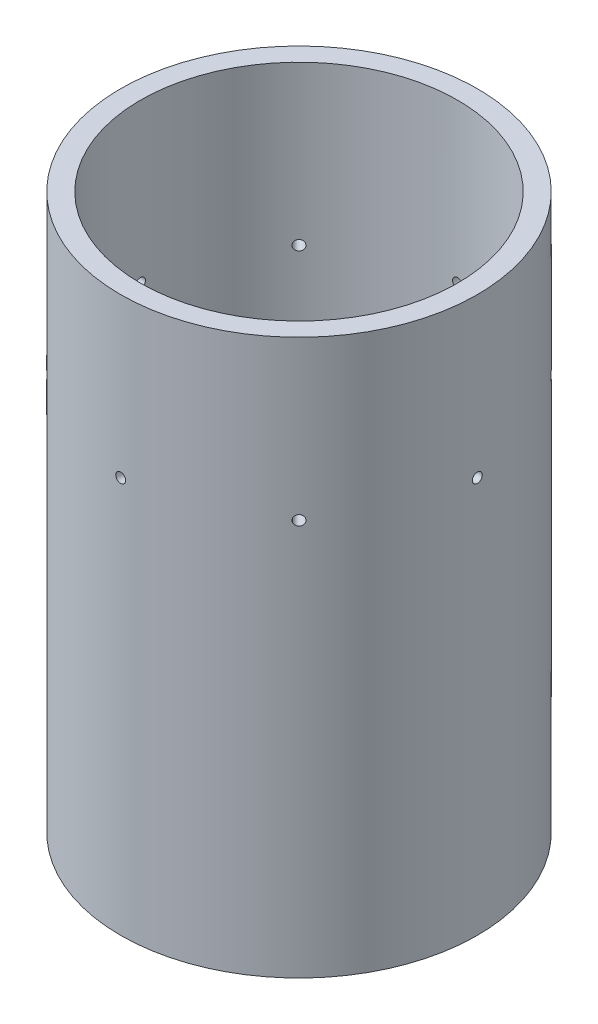
SolidWorks part; units mm, degrees
material "PVC Rigid"
ref_plane "Front Plane" through (0, 0, 0) normal (0, 0, 1) x (1, 0, 0)
ref_plane "Top Plane" through (0, 0, 0) normal (0, 1, 0) x (1, 0, 0)
ref_plane "Right Plane" through (0, 0, 0) normal (1, 0, 0) x (0, 0, -1)
sketch "Sketch1" plane through (0, 0, 0) normal (0, 1, 0) x (1, 0, 0)
  circle A0 centre (0, 0) radius 50.8
  circle A1 centre (0, 0) radius 57.15
  dimension "D1" = 101.6
  dimension "D2" = 6.35
extrude "Boss-Extrude1" add sketch "Sketch1" along normal blind 177.8
ref_plane "Plane1" through (0, 0, 53.975) normal (0, 0, 1) x (1, 0, 0)
sketch "Sketch3" plane through (0, 0, 53.975) normal (0, 0, 1) x (1, 0, 0)
  line L0 (-57.15, 0) -> (57.15, 0) construction
  circle A0 centre (0, 127) radius 1.5875
  dimension "D1" = 3.175
  dimension "D2" = 127
extrude "Cut-Extrude1" cut sketch "Sketch3" against normal mid plane 12.7
pattern_circular "CirPattern1" count 8 over 360 about axis through (0, 177.8, 0) along (0, 1, 0) of "Cut-Extrude1"
